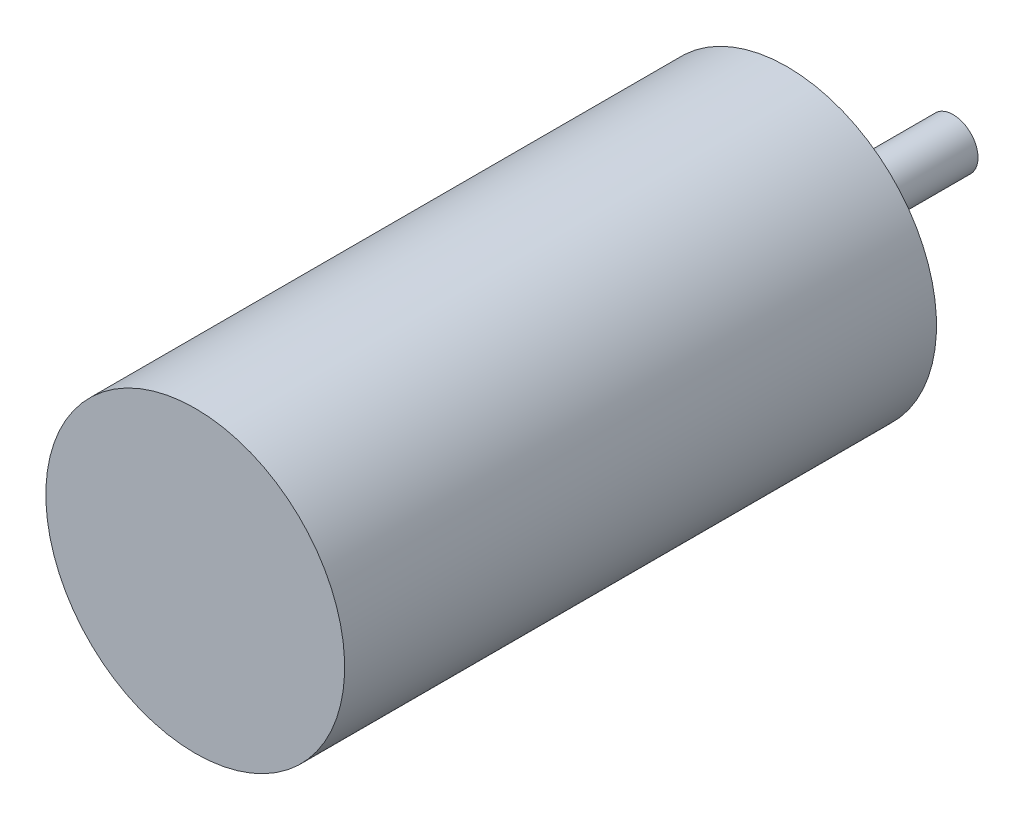
SolidWorks part; units mm, degrees
ref_plane "Front Plane" through (0, 0, 0) normal (0, 0, 1) x (1, 0, 0)
ref_plane "Top Plane" through (0, 0, 0) normal (0, 1, 0) x (1, 0, 0)
ref_plane "Right Plane" through (0, 0, 0) normal (1, 0, 0) x (0, 0, -1)
sketch "Sketch1" plane through (0, 0, 0) normal (1, 0, 0) x (0, 0, -1)
  line L0 (0, 0) -> (0, 18)
  line L1 (0, 18) -> (71.3, 18)
  line L2 (71.3, 18) -> (71.3, 6.5)
  line L3 (71.3, 6.5) -> (72.5, 6.5)
  line L4 (72.5, 6.5) -> (72.5, 4.8636)
  line L5 (72.5, 4.8636) -> (74.65, 4.8636)
  line L6 (74.65, 4.8636) -> (74.65, 3)
  line L7 (74.65, 3) -> (91.3, 3)
  line L8 (91.3, 3) -> (91.3, 0)
  line L9 (91.3, 0) -> (0, 0)
  dimension "D1" = 18
  dimension "D2" = 1.2
  dimension "D3" = 3.35
  dimension "D4" = 20
  dimension "D5" = 71.3
  dimension "D6" = 6.5
  dimension "D7" = 3
revolve "Revolve1" add sketch "Sketch1" angle 360 about L9
sketch "Sketch2" plane through (0, 0, -71.3) normal (0, 0, -1) x (-1, 0, 0)
  line L0 (0, 0) -> (0, 18) construction
  line L1 (0, 0) -> (18, 0) construction
  circle A0 centre (0, 0) radius 18 construction
  circle A1 centre (0, 9.5) radius 1.25
  circle A2 centre (8.2272, 4.75) radius 1.25
  circle A3 centre (8.2272, -4.75) radius 1.25
  circle A4 centre (0, -9.5) radius 1.25
  circle A5 centre (-8.2272, -4.75) radius 1.25
  circle A6 centre (-8.2272, 4.75) radius 1.25
  point P21 (0, 0)
  dimension "D1" = 2.5
  dimension "D2" = 9.5
  dimension "D3" = 6
extrude "Cut-Extrude1" cut sketch "Sketch2" against normal blind 6.5
